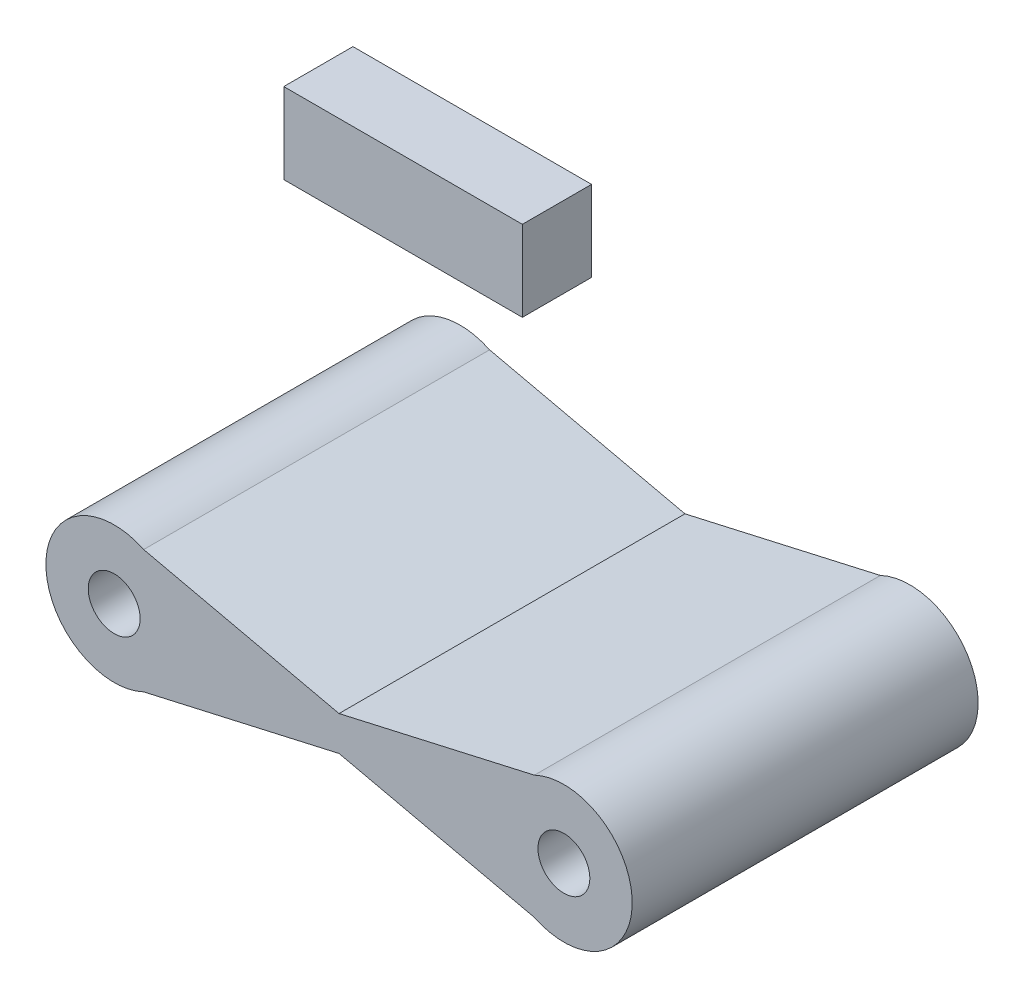
SolidWorks part; units mm, degrees
ref_plane "Front Plane" through (0, 0, 0) normal (0, 0, 1) x (1, 0, 0)
ref_plane "Top Plane" through (0, 0, 0) normal (0, 1, 0) x (1, 0, 0)
ref_plane "Right Plane" through (0, 0, 0) normal (1, 0, 0) x (0, 0, -1)
sketch "Sketch1" plane through (0, 0, 0) normal (0, 0, 1) x (1, 0, 0)
  line L0 (0, 2.475) -> (6.5, 1)
  line L1 (0, 1) -> (13, 1)
  line L2 (0, 1) -> (0, 0)
  line L3 (0, 0) -> (13, 0)
  line L4 (13, 1) -> (13, 0)
  line L5 (6.5, 1) -> (13, 2.475)
  line L6 (13, -1.475) -> (6.5, 0)
  line L7 (0, -1.475) -> (6.5, 0)
  circle A0 centre (0, 0.5) radius 1.975
  circle A1 centre (13, 0.5) radius 1.975
  circle A2 centre (0, 0.5) radius 0.75
  circle A3 centre (13, 0.5) radius 0.75
  dimension "D3" = 3.95
  dimension "D4" = 1.5
  dimension "D1" = 1
  dimension "D2" = 13
extrude "Boss-Extrude1" add sketch "Sketch1" along normal blind 10 contours L1 A0 L0 L7 L3 L2 | L3 A0 L1 L2 | A1 L1 A0 L3 | A0 L1 L0 | A1 L5 L1 | L5 A1 L1 L4 L3 L6 | L1 A1 L3 L4 | A1 L3 L6 | A0 L7 L3 | L5 A1 | L6 A1 | L7 A0 | L0 A0
sketch "Sketch3" plane through (0, 0, 0) normal (0, 0, -1) x (-1, 0, 0)
  line L1 (-3.7995, 7.898) -> (3.0979, 7.898)
  line L2 (-3.7995, 7.898) -> (-3.7995, 5.5681)
  line L3 (-3.7995, 5.5681) -> (3.0979, 5.5681)
  line L4 (3.0979, 7.898) -> (3.0979, 5.5681)
extrude "Boss-Extrude3" add sketch "Sketch3" against normal blind 2 separate body
